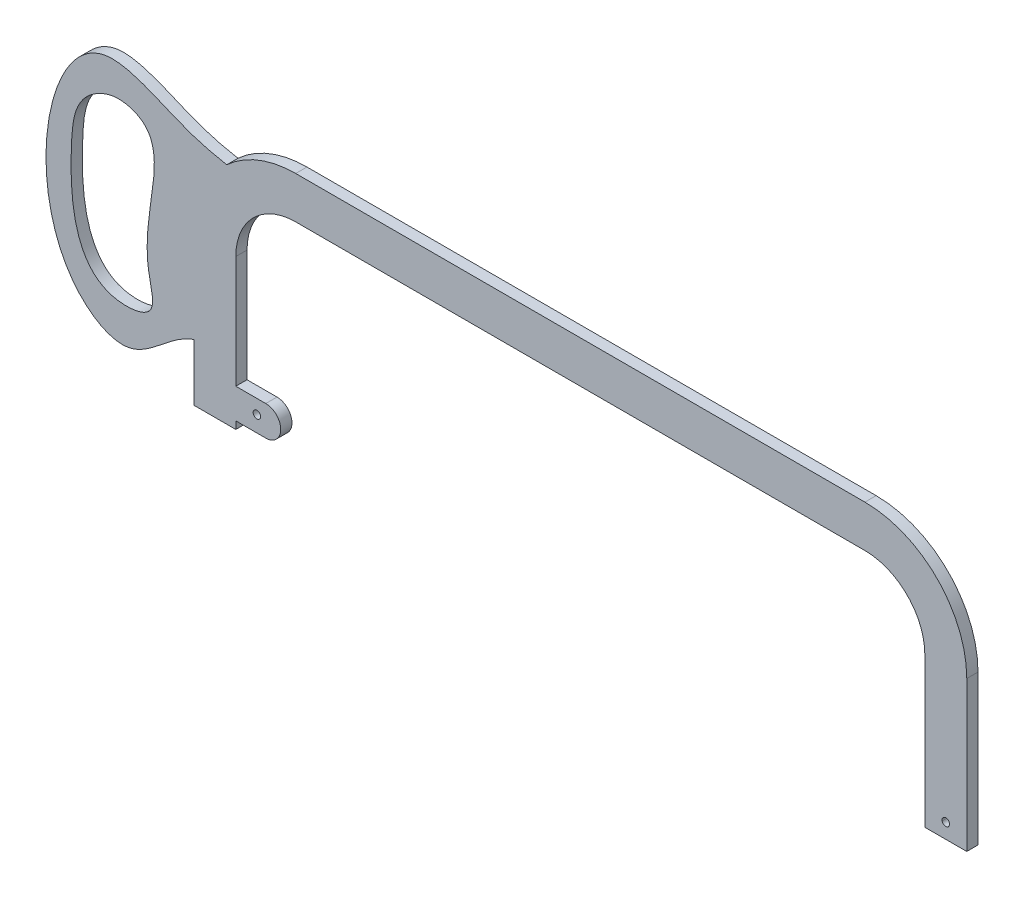
SolidWorks part; units mm, degrees
material "AISI 1020 Steel, Cold Rolled"
ref_plane "Front Plane" through (0, 0, 0) normal (0, 0, 1) x (1, 0, 0)
ref_plane "Top Plane" through (0, 0, 0) normal (0, 1, 0) x (1, 0, 0)
ref_plane "Right Plane" through (0, 0, 0) normal (1, 0, 0) x (0, 0, -1)
sketch "Sketch2" plane through (0, 0, 0) normal (0, 0, 1) x (1, 0, 0)
  line L0 (-176.2528, 0) -> (-176.2528, 63.5)
  line L1 (-150.8528, 88.9) -> (90.4472, 88.9)
  line L2 (115.8472, 63.5) -> (115.8472, 0)
  line L3 (115.8472, 0) -> (133.6272, 0)
  line L4 (133.6272, 0) -> (133.6272, 63.5)
  line L5 (90.4472, 106.68) -> (-150.8528, 106.68)
  line L6 (-194.0328, 63.5) -> (-194.0328, 0)
  line L7 (-194.0328, 0) -> (-176.2528, 0)
  arc A0 (-176.2528, 63.5) -> (-150.8528, 88.9) centre (-150.8528, 63.5) cw
  arc A1 (115.8472, 63.5) -> (90.4472, 88.9) centre (90.4472, 63.5) ccw
  arc A2 (-194.0328, 63.5) -> (-150.8528, 106.68) centre (-150.8528, 63.5) cw
  arc A3 (133.6272, 63.5) -> (90.4472, 106.68) centre (90.4472, 63.5) ccw
  dimension "D4" = 63.5
  dimension "D1" = 17.78
  dimension "D2" = 17.78
  dimension "D3" = 241.3
extrude "Extrude1" add sketch "Sketch2" along normal mid plane 4.7625
sketch "Sketch4" plane through (0, 0, 2.3813) normal (0, 0, 1) x (1, 0, 0)
  line L0 (-176.2528, 3.175) -> (-163.5528, 3.175)
  line L1 (-176.2528, 0) -> (-176.2528, 63.5) construction
  line L2 (-176.2528, 15.875) -> (-163.5528, 15.875)
  line L3 (-194.0328, 0) -> (-176.2528, 0) construction
  line L4 (-176.2528, 15.875) -> (-176.2528, 3.175)
  arc A0 (-163.5528, 3.175) -> (-163.5528, 15.875) centre (-163.5528, 9.525) ccw
  dimension "D1" = 12.7
  dimension "D2" = 3.175
  dimension "D3" = 12.7
extrude "Extrude2" add sketch "Sketch4" against normal up to surface (4.7625 mm away) up to face at (-30.2028, 56.1306, -2.3813)
sketch "Sketch5" plane through (0, 0, 2.3813) normal (0, 0, 1) x (1, 0, 0)
  line L0 (133.6272, 0) -> (133.6272, 63.5) construction
  circle A0 centre (-167.3363, 9.9386) radius 1.5875
  circle A1 centre (124.7372, 6.35) radius 1.5875
  arc A2 (115.8472, 63.5) -> (90.4472, 88.9) centre (90.4472, 63.5) ccw construction
  point P4 (90.4472, 63.5)
  dimension "D1" = 3.175
  dimension "D2" = 57.15
  dimension "D3" = 8.89
extrude "Cut-Extrude1" cut sketch "Sketch5" against normal through all
sketch "Sketch6" plane through (0, 0, 2.3813) normal (0, 0, 1) x (1, 0, 0)
  line L1 (-163.5001, 92.9767) -> (-185.371, 71.1058)
  line L2 (-185.371, 71.1058) -> (-185.371, 24.5413)
  spline S0 degree 3 poles (-163.5001, 92.9767) (-174.2158, 94.2301) (-196.7764, 96.8689) (-252.8592, 130.1247) (-269.4265, 29.7933) (-217.0907, -1.2909) (-200.7578, 26.3378) (-186.8997, 24.7198) (-185.371, 24.5413) knots 0 0 0 0 0.145422 0.306167 0.711218 0.81884 0.980016 1 1 1 1
  spline S1 degree 3 poles (-229.0238, 98.1269) (-244.4394, 89.2831) (-247.2836, 60.1055) (-244.9157, 18.8537) (-208.0817, 23.1237) (-220.298, 55.3932) (-201.0956, 90.7405) (-229.0238, 98.1269) (-244.4394, 89.2831) (-247.2836, 60.1055) knots -0.440904 -0.140512 -0.093904 0 0.110818 0.392382 0.473965 0.559096 0.859488 0.906096 1 1.110818 1.392382 1.473965 only from (-241.012, 88.8095) to (-241.012, 88.8095)
  point P2 (-249.3752, 94.5849)
extrude "Extrude3" add sketch "Sketch6" against normal up to surface (4.7625 mm away)
ref_plane "Plane1" through (123.19, 0, 0) normal (1, 0, 0) x (0, 0, -1)
split line "Split Line1"
sketch "Sketch7" plane through (0, 0, 0) normal (0, 0, 1) x (1, 0, 0)
  line L0 (90.4472, 63.5) -> (90.4472, 129.4025)
  line L1 (90.4472, 63.5) -> (160.7609, 63.5)
  arc A0 (115.8472, 63.5) -> (90.4472, 88.9) centre (90.4472, 63.5) ccw construction
  arc A1 (115.8472, 63.5) -> (90.4472, 88.9) centre (90.4472, 63.5) ccw
